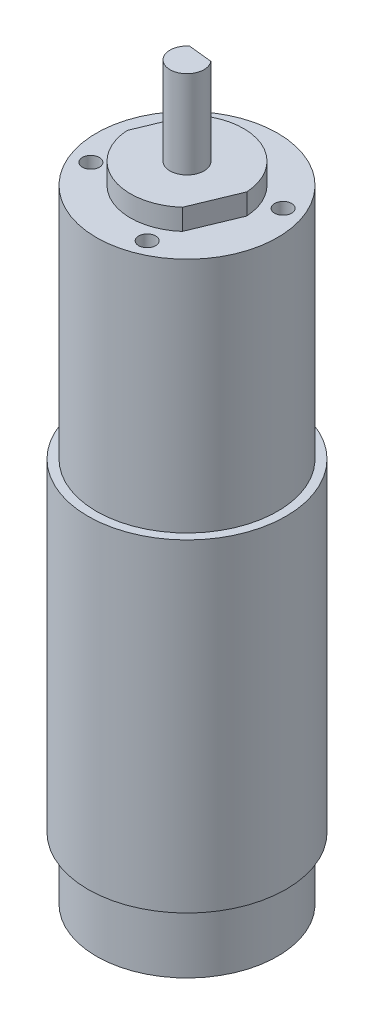
SolidWorks part; units mm, degrees
ref_plane "Front Plane" through (0, 0, 0) normal (0, 0, 1) x (1, 0, 0)
ref_plane "Top Plane" through (0, 0, 0) normal (0, 1, 0) x (1, 0, 0)
ref_plane "Right Plane" through (0, 0, 0) normal (1, 0, 0) x (0, 0, -1)
sketch "Sketch1" plane through (0, 0, 0) normal (0, 1, 0) x (1, 0, 0)
  circle A0 centre (0, 0) radius 17.5
extrude "Boss-Extrude1" add sketch "Sketch1" along normal blind 57.1
sketch "Sketch2" plane through (0, 0, 0) normal (0, -1, 0) x (1, 0, 0)
  circle A0 centre (0, 0) radius 16
extrude "Boss-Extrude2" add sketch "Sketch2" along normal blind 11
sketch "Sketch3" plane through (0, 57.1, 0) normal (0, 1, 0) x (1, 0, 0)
  circle A0 centre (0, 0) radius 16
extrude "Boss-Extrude3" add sketch "Sketch3" along normal blind 41.9
sketch "Sketch4" plane through (0, 99, 0) normal (0, 1, 0) x (1, 0, 0)
  circle A0 centre (4.9703, -12.0123) radius 1.5
  circle A1 centre (-12.0123, -4.9703) radius 1.5
  circle A2 centre (-4.9703, 12.0123) radius 1.5
  circle A3 centre (12.0123, 4.9703) radius 1.5
  circle A4 centre (0, 0) radius 10
  point P5 (0, 0)
  point P8 (0, 0)
  point P16 (0, 0)
  dimension "D2" = 4
extrude "Cut-Extrude2" cut sketch "Sketch4" against normal blind 15 contours A3 | A2 | A1 | A0
sketch "Sketch6" plane through (0, 99, 0) normal (0, 1, 0) x (1, 0, 0)
  line L2 (-9.9832, -0.5792) -> (-6.644, 7.4738)
  line L3 (6.644, -7.4738) -> (9.9832, 0.5792)
  arc A0 (-9.9832, -0.5792) -> (6.644, -7.4738) centre (0, 0) ccw
  arc A1 (9.9832, 0.5792) -> (-6.644, 7.4738) centre (0, 0) ccw
  point P10 (-8.3136, 3.4473)
  dimension "D1" = 20
extrude "Boss-Extrude5" add sketch "Sketch6" along normal blind 3.7
sketch "Sketch7" plane through (0, 102.7, 0) normal (0, 1, 0) x (1, 0, 0)
  circle A0 centre (0, 0) radius 3
extrude "Boss-Extrude6" add sketch "Sketch7" along normal blind 15.5
sketch "Sketch8" plane through (0, 118.2, 0) normal (0, 1, 0) x (1, 0, 0)
  line L2 (-1.8839, 2.3348) -> (2.3348, 1.8839)
  circle A0 centre (0, 0) radius 3 construction
  arc A1 (2.3348, 1.8839) -> (-1.8839, 2.3348) centre (0, 0) ccw
  circle M1 centre (0, 0) radius 3
extrude "Cut-Extrude3" cut sketch "Sketch8" against normal blind 10 contours L2 M1
